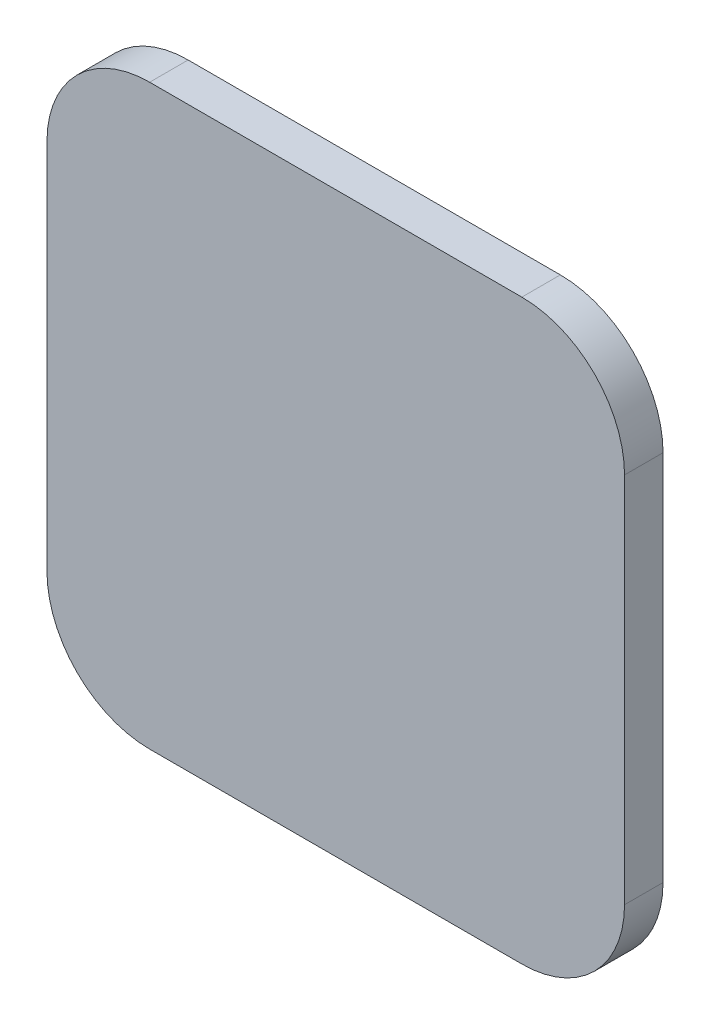
SolidWorks part; units mm, degrees
material "AISI 316 Stainless Steel Sheet (SS)"
ref_plane "Front Plane" through (0, 0, 0) normal (0, 0, 1) x (1, 0, 0)
ref_plane "Top Plane" through (0, 0, 0) normal (0, 1, 0) x (1, 0, 0)
ref_plane "Right Plane" through (0, 0, 0) normal (1, 0, 0) x (0, 0, -1)
sketch "Sketch1" plane through (0, 0, 0) normal (0, 0, 1) x (1, 0, 0)
  line L0 (1213.5748, 135) -> (1242.5748, 135) construction
  line L1 (1250.5748, 143) -> (1250.5748, 172) construction
  line L2 (1242.5748, 180) -> (1213.5748, 180) construction
  line L3 (1205.5748, 172) -> (1205.5748, 143) construction
  line L4 (1213.5748, 135) -> (1242.5748, 135)
  line L5 (1250.5748, 143) -> (1250.5748, 172)
  line L6 (1242.5748, 180) -> (1213.5748, 180)
  line L7 (1205.5748, 172) -> (1205.5748, 143)
  arc A0 (1205.5748, 143) -> (1213.5748, 135) centre (1213.5748, 143) ccw construction
  arc A1 (1242.5748, 135) -> (1250.5748, 143) centre (1242.5748, 143) ccw construction
  arc A2 (1250.5748, 172) -> (1242.5748, 180) centre (1242.5748, 172) ccw construction
  arc A3 (1213.5748, 180) -> (1205.5748, 172) centre (1213.5748, 172) ccw construction
  arc A4 (1205.5748, 143) -> (1213.5748, 135) centre (1213.5748, 143) ccw
  arc A5 (1242.5748, 135) -> (1250.5748, 143) centre (1242.5748, 143) ccw
  arc A6 (1250.5748, 172) -> (1242.5748, 180) centre (1242.5748, 172) ccw
  arc A7 (1213.5748, 180) -> (1205.5748, 172) centre (1213.5748, 172) ccw
extrude "Boss-Extrude1" add sketch "Sketch1" against normal blind 3
